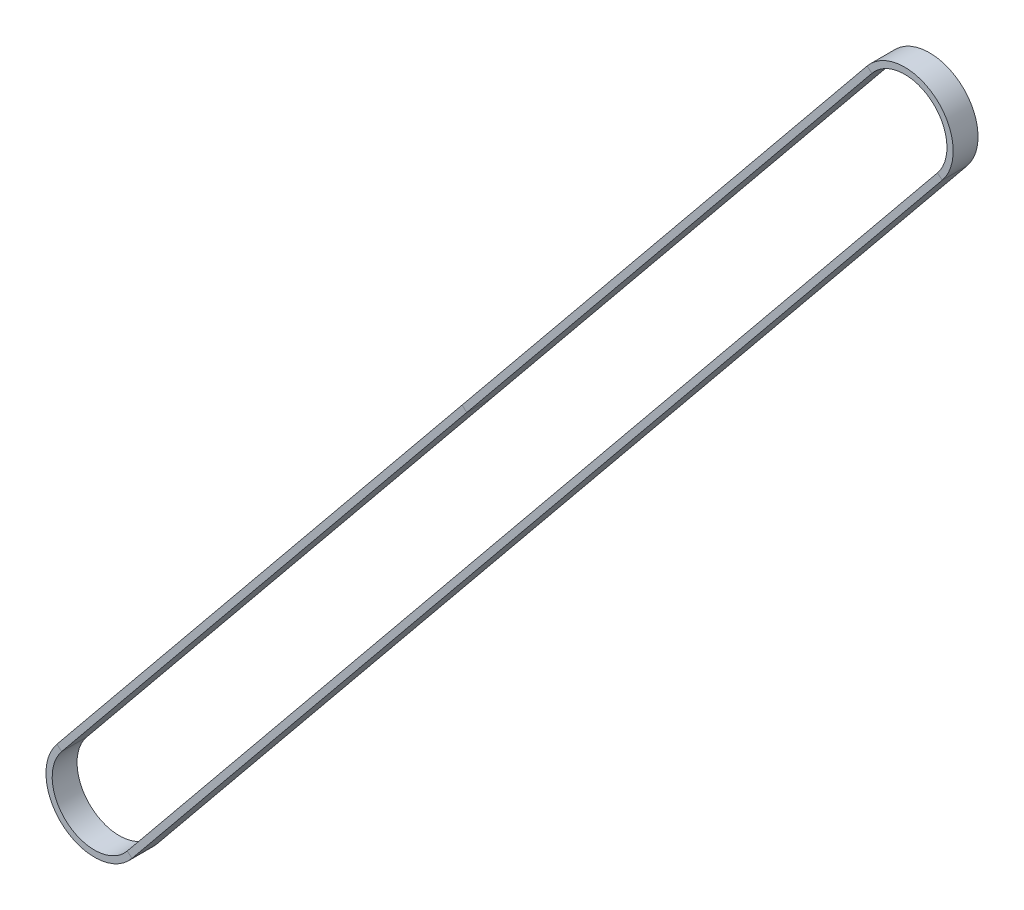
SolidWorks part; units mm, degrees
material "POLYURETHANE (11671)"
ref_plane "Front Plane" through (0, 0, 0) normal (0, 0, 1) x (1, 0, 0)
ref_plane "Top Plane" through (0, 0, 0) normal (0, 1, 0) x (1, 0, 0)
ref_plane "Right Plane" through (0, 0, 0) normal (1, 0, 0) x (0, 0, -1)
sketch "Sketch1" plane through (0, 0, 0) normal (0, 0, 1) x (1, 0, 0)
  line L0 (187.5866, 245.9004) -> (-7.9012, 6.4506)
  line L1 (7.9012, -6.4506) -> (203.389, 232.9991)
  circle A0 centre (0, 0) radius 10.2 construction
  arc A1 (-7.9012, 6.4506) -> (7.9012, -6.4506) centre (0, 0) ccw
  circle A2 centre (195.4878, 239.4498) radius 10.2 construction
  arc A3 (203.389, 232.9991) -> (187.5866, 245.9004) centre (195.4878, 239.4498) ccw
sketch3d "3DSketch1"
  line L0 (187.5866, 245.9004, 0) -> (-7.9012, 6.4506, 0) construction
  point P0 (89.8427, 126.1755, 0)
ref_plane "Plane2" through (89.8427, 126.1755, 0) normal (-0.6324, -0.7746, 0) x (-0.7746, 0.6324, 0)
sketch "Sketch2" plane through (89.8427, 126.1755, 0) normal (-0.6324, -0.7746, 0) x (-0.7746, 0.6324, 0)
  line L0 (1.5, -3) -> (0, -3)
  line L1 (1.5, -3) -> (1.5, 3)
  line L2 (0, -3) -> (0, 3)
  line L3 (1.5, 3) -> (0, 3)
  line L4 (1.5, -3) -> (0, 3) construction
  line L5 (0, -3) -> (1.5, 3) construction
  point P0 (2.398, -3.0679)
  point P1 (0.75, 0)
  point P2 (0, 0)
  dimension "D1" = 6
  dimension "D2" = 1.5
sweep "Sweep1" add profiles "Sketch2" path "Sketch1"
